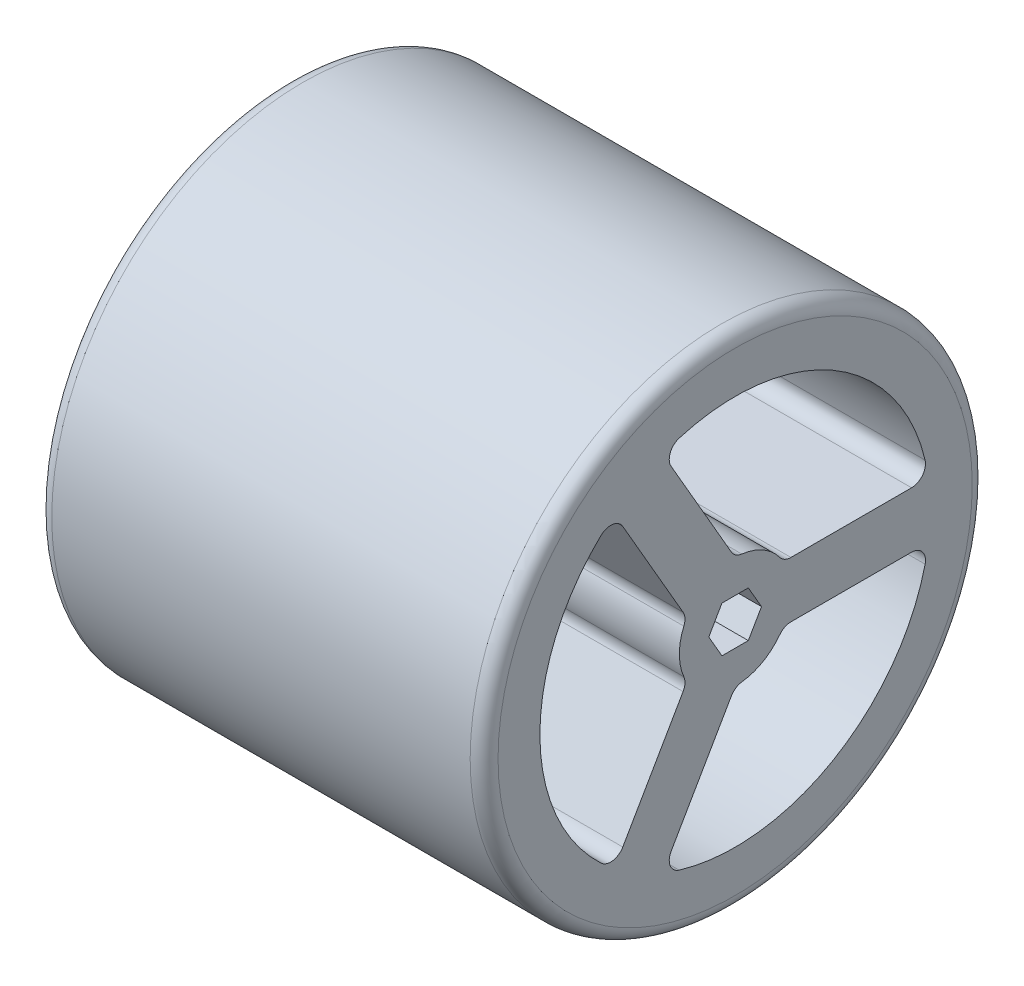
SolidWorks part; units mm, degrees
ref_plane "Front Plane" through (0, 0, 0) normal (0, 0, 1) x (1, 0, 0)
ref_plane "Top Plane" through (0, 0, 0) normal (0, 1, 0) x (1, 0, 0)
ref_plane "Right Plane" through (0, 0, 0) normal (1, 0, 0) x (0, 0, -1)
sketch "Sketch1" plane through (0, 0, 0) normal (1, 0, 0) x (0, 0, -1)
  line L0 (0, 0) -> (14.2875, 0) construction
  line L1 (0.75, -1.299) -> (1.5, 0)
  line L2 (1.5, 0) -> (0.75, 1.299)
  line L3 (0.75, 1.299) -> (-0.75, 1.299)
  line L4 (-0.75, 1.299) -> (-1.5, 0)
  line L5 (-1.5, 0) -> (-0.75, -1.299)
  line L6 (-0.75, -1.299) -> (0.75, -1.299)
  line L7 (3.175, 1.5875) -> (10.0402, 1.5875)
  line L8 (3.175, -1.5875) -> (10.0402, -1.5875)
  line L9 (-0.2127, -3.5434) -> (-3.6453, -9.4888)
  line L10 (0, 0) -> (-7.1438, -12.3733) construction
  line L11 (-2.9623, -1.9559) -> (-6.3949, -7.9013)
  line L12 (-2.9623, 1.9559) -> (-6.3949, 7.9013)
  line L13 (0, 0) -> (-7.1437, 12.3733) construction
  line L14 (-0.2127, 3.5434) -> (-3.6453, 9.4888)
  line L15 (0, 0) -> (2.7496, -1.5875) construction
  line L16 (0, 0) -> (-2.7496, -1.5875) construction
  circle A0 centre (0, 0) radius 14.2875
  arc A1 (-7.6271, 8.0817) -> (-7.6271, -8.0817) centre (0, 0) ccw
  arc A2 (-2.9198, 1.2472) -> (-2.9198, -1.2472) centre (0, 0) ccw
  circle A3 centre (0, 0) radius 1.299 construction
  arc A4 (2.54, 1.905) -> (0.3798, 3.1522) centre (0, 0) ccw
  arc A5 (10.8126, 2.5644) -> (-3.1854, 10.6462) centre (0, 0) ccw
  arc A6 (0.3798, -3.1522) -> (2.54, -1.905) centre (0, 0) ccw
  arc A7 (-3.1854, -10.6462) -> (10.8126, -2.5644) centre (0, 0) ccw
  arc A8 (-0.2127, -3.5434) -> (0.3798, -3.1522) centre (0.4747, -3.9403) cw
  arc A9 (-3.6453, -9.4888) -> (-3.1854, -10.6462) centre (-2.9579, -9.8857) ccw
  arc A10 (10.0402, -1.5875) -> (10.8126, -2.5644) centre (10.0402, -2.3812) cw
  arc A11 (3.175, -1.5875) -> (2.54, -1.905) centre (3.175, -2.3813) ccw
  arc A12 (-0.2127, 3.5434) -> (0.3798, 3.1522) centre (0.4747, 3.9403) ccw
  arc A13 (3.175, 1.5875) -> (2.54, 1.905) centre (3.175, 2.3813) cw
  arc A14 (10.0402, 1.5875) -> (10.8126, 2.5644) centre (10.0402, 2.3812) ccw
  arc A15 (-3.1854, 10.6462) -> (-3.6453, 9.4888) centre (-2.9579, 9.8857) ccw
  arc A16 (-7.6271, -8.0817) -> (-6.3949, -7.9013) centre (-7.0823, -7.5045) ccw
  arc A17 (-2.9623, -1.9559) -> (-2.9198, -1.2472) centre (-3.6497, -1.559) ccw
  arc A18 (-2.9198, 1.2472) -> (-2.9623, 1.9559) centre (-3.6497, 1.559) ccw
  arc A19 (-6.3949, 7.9013) -> (-7.6271, 8.0817) centre (-7.0823, 7.5045) ccw
  point P36 (2.7496, -1.5875)
  point P41 (2.7496, 1.5875)
  point P44 (10.9985, 1.5875)
  point P51 (-2.7496, -1.5875)
  dimension "D1" = 28.575
  dimension "D2" = 3.175
  dimension "D8" = 6.35
  dimension "D9" = 0.7937
  dimension "D3" = 3
  dimension "D4" = 1.5875
  dimension "D5" = 1.5875
  dimension "D7" = 120
  dimension "D6" = 3
extrude "Boss-Extrude1" add sketch "Sketch1" along normal mid plane 25.4
fillet "Fillet1" radius 0.7937 2 edges at (-12.7, 0, -14.2875) (12.7, 0, -14.2875)
